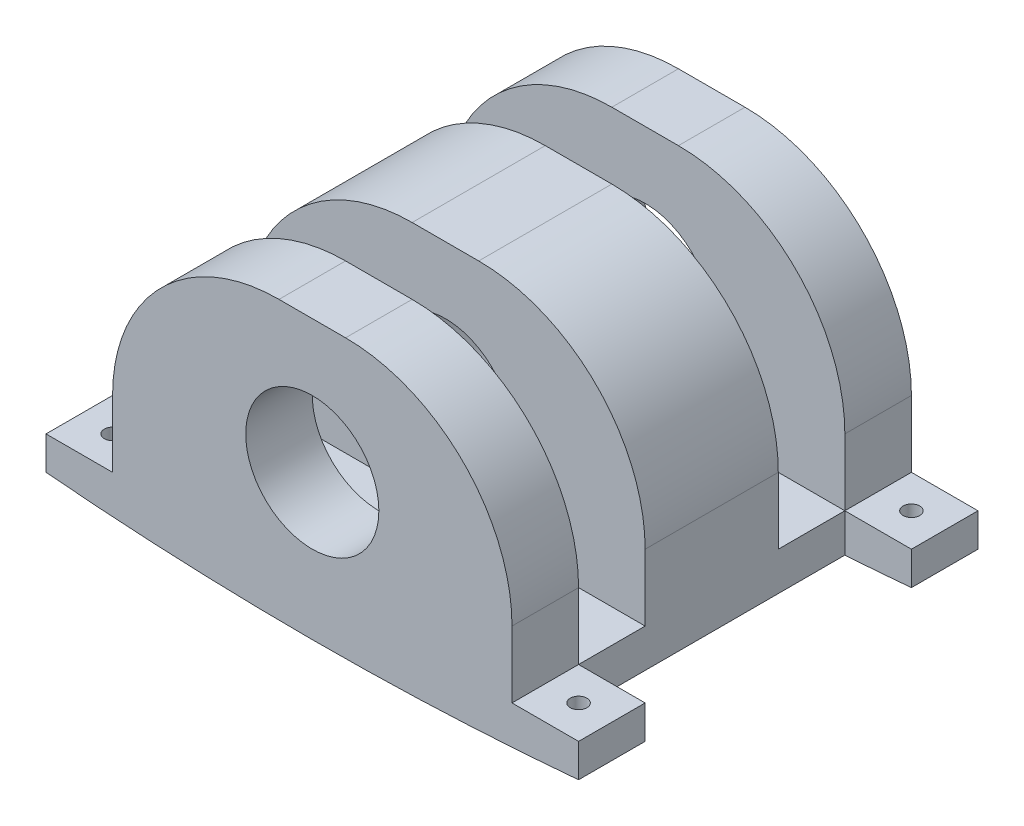
SolidWorks part; units mm, degrees
material "7075-T6 (SN)"
ref_plane "Front Plane" through (0, 0, 0) normal (0, 0, 1) x (1, 0, 0)
ref_plane "Top Plane" through (0, 0, 0) normal (0, 1, 0) x (1, 0, 0)
ref_plane "Right Plane" through (0, 0, 0) normal (1, 0, 0) x (0, 0, -1)
sketch "Sketch1" plane through (0, 0, 0) normal (0, 0, 1) x (1, 0, 0)
  line L1 (-76.2, -50.8) -> (76.2, -50.8) construction
  line L2 (-76.2, -38.1) -> (-76.2, -12.7)
  line L3 (-12.7, 50.8) -> (12.7, 50.8)
  line L4 (76.2, -38.1) -> (76.2, -12.7)
  line L5 (-76.2, -50.8) -> (76.2, 50.8) construction
  line L6 (-76.2, 50.8) -> (76.2, -50.8) construction
  line L7 (-76.2, -50.8) -> (-101.6, -50.8) construction
  line L9 (-76.2, -38.1) -> (-101.6, -38.1)
  line L10 (-101.6, -50.8) -> (-101.6, -38.1)
  line L11 (76.2, -50.8) -> (101.6, -50.8) construction
  line L13 (76.2, -38.1) -> (101.6, -38.1)
  line L14 (101.6, -50.8) -> (101.6, -38.1)
  arc A0 (76.2, -12.7) -> (12.7, 50.8) centre (12.7, -12.7) ccw
  arc A1 (-12.7, 50.8) -> (-76.2, -12.7) centre (-12.7, -12.7) ccw
  circle A2 centre (0, 0) radius 25.4
  arc A3 (-101.6, -50.8) -> (101.6, -50.8) centre (0, 1094.7031) ccw
  point P0 (0, 0)
  dimension "D3" = 63.5
  dimension "D8" = 50.8
  dimension "D9" = 1150
  dimension "D1" = 152.4
  dimension "D2" = 101.6
  dimension "D4" = 12.7
  dimension "D5" = 12.7
  dimension "D6" = 25.4
  dimension "D7" = 25.4
extrude "Boss-Extrude1" add sketch "Sketch1" along normal blind 152.4
sketch "Sketch3" plane through (0, 0, 0) normal (1, 0, 0) x (0, 0, -1)
  line L0 (-152.4, -38.1) -> (0, -38.1) construction
  line L1 (-127, -38.1) -> (-101.6, -38.1)
  line L2 (-127, -38.1) -> (-127, 50.8)
  line L3 (-127, 50.8) -> (-101.6, 50.8)
  line L4 (-101.6, -38.1) -> (-101.6, 50.8)
  line L5 (-152.4, 50.8) -> (0, 50.8) construction
  line L6 (-152.4, 50.8) -> (-152.4, -12.7) construction
  line L7 (-50.8, -38.1) -> (-25.4, -38.1)
  line L8 (-50.8, -38.1) -> (-50.8, 50.8)
  line L9 (-50.8, 50.8) -> (-25.4, 50.8)
  line L10 (-25.4, -38.1) -> (-25.4, 50.8)
  dimension "D1" = 25.4
  dimension "D2" = 25.4
  dimension "D3" = 50.8
  dimension "D4" = 25.4
extrude "Cut-Extrude1" cut sketch "Sketch3" against normal through all both and the other way through all
sketch "Sketch4" plane through (0, -38.1, 0) normal (0, 1, 0) x (1, 0, 0)
  line L0 (-101.6, -152.4) -> (-101.6, 0) construction
  line L1 (101.6, -152.4) -> (101.6, 0) construction
  line L2 (-76.2, 0) -> (-101.6, 0) construction
  line L3 (-76.2, -101.6) -> (-76.2, -50.8) construction
  line L4 (-101.6, -25.4) -> (-76.2, -25.4)
  line L5 (-101.6, -25.4) -> (-101.6, -127)
  line L6 (-101.6, -127) -> (-76.2, -127)
  line L7 (-76.2, -25.4) -> (-76.2, -127)
  line L8 (-76.2, -152.4) -> (-101.6, -152.4) construction
  line L9 (0, -55) -> (0, 55) construction
  line L10 (101.6, -127) -> (76.2, -127)
  line L11 (76.2, -25.4) -> (76.2, -127)
  line L12 (101.6, -25.4) -> (76.2, -25.4)
  line L13 (101.6, -25.4) -> (101.6, -127)
  point P0 (-88.9, -12.7)
  point P2 (-88.9, -139.7)
  point P3 (88.9, -12.7)
  point P5 (88.9, -139.7)
  dimension "D1" = 12.7
  dimension "D2" = 12.7
  dimension "D3" = 12.7
  dimension "D4" = 25.4
  dimension "D5" = 25.4
hole_wizard "1/4 (0.25) Diameter Hole1" positions "Sketch5" profile "Sketch6" hole size "1/4" standard "ANSI Inch" end condition through all
sketch "Sketch5" plane through (0, -38.1, 0) normal (0, 1, 0) x (1, 0, 0)
  point P3 (-88.9, -12.7)
  point P6 (-88.9, -139.7)
  point P9 (88.9, -12.7)
  point P15 (88.9, -139.7)
sketch "Sketch6" plane through (-88.9, -38.1, 12.7) normal (1, 0, 0) x (0, 0, 1)
  line L0 (0, 0) -> (0, 17.1969)
  line L1 (0, 17.1969) -> (3.175, 17.1969)
  line L2 (3.175, 17.1969) -> (3.175, 0)
  line L5 (3.175, 0) -> (0, 0)
  line L11 (0, -6.35) -> (0, 107.95) construction
  dimension "Thru Hole Dia." = 6.35
  dimension "Thru Hole Depth" = 17.1969
extrude "Cut-Extrude2" cut sketch "Sketch4" against normal through all
